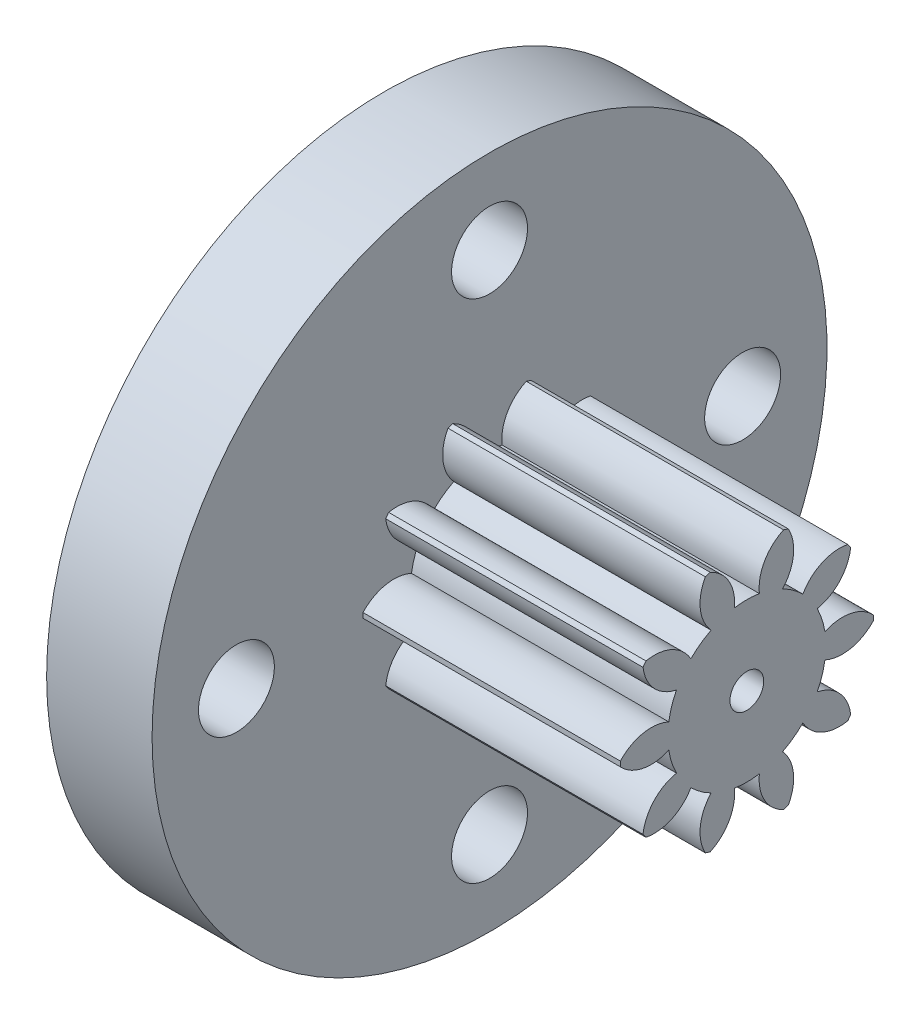
SolidWorks part; units mm, degrees
ref_plane "Plane1" through (0, 0, 0) normal (0, 0, 1) x (1, 0, 0)
ref_plane "Plane2" through (0, 0, 0) normal (0, 1, 0) x (1, 0, 0)
ref_plane "Plane3" through (0, 0, 0) normal (1, 0, 0) x (0, 0, -1)
sketch "HoldingSke" plane through (0, 0, 0) normal (0, 1, 0) x (1, 0, 0)
  line L0 (0, 0) -> (1.9696, -0.3473)
  line L1 (-15, 0) -> (100, 0) construction
  line L2 (0, 0) -> (-2.1039, 2.3779)
  line L3 (0, 0) -> (-11.863, 4.5341)
  line L4 (0, 0) -> (8.5048, 1.4996)
  line L5 (0, 0) -> (-46.8476, -17.4728)
  line L6 (0, 0) -> (-6.6317, -4.4744)
  line L7 (-2.1039, 2.3779) -> (8.6586, 51.2059)
  line L8 (-76.2, 54.61) -> (-76.1, 54.61)
  line L9 (-71.009, 38.7566) -> (-53.1078, 45.2721)
  line L10 (-76.2, 71.12) -> (104.1128, 71.12)
  line L11 (0, 0) -> (-8, 0)
  line L12 (-76.2, 101.6) -> (-76.181, 101.6)
  line L13 (24.9733, 27.94) -> (52.9518, 28.4284)
  line L14 (24.9733, 27.94) -> (24.9743, 27.94)
  line L15 (24.9733, 27.94) -> (100.4006, 29.5858)
  line L16 (-63.627, -0.5) -> (-12.827, -0.5)
  circle A0 centre (0, 0) radius 0.4
  circle A1 centre (0, 0) radius 1.874
  circle A2 centre (0, 0) radius 37.5
  circle A3 centre (0, 0) radius 0.4
  dimension "MHD" = 3.748
  dimension "Hub_dia" = 75
  dimension "Bore" = 0.8
  dimension "MBD" = 0.8
  dimension "Num_teeth" = 10
  dimension "Pitch" = 2
  dimension "Overall_len" = 50
  dimension "Show_teeth" = 10
  dimension "Thickness" = 8
  dimension "OAL" = 50.0001
  dimension "T_dim" = 0.1
  dimension "Ap" = 20
  dimension "H" = 19.05
  dimension "Pitch_radius" = 180.3128
  dimension "Width" = 8
  dimension "Backlash" = 0.019
  dimension "Addendum_fac" = 1
  dimension "Dedendum_fac" = 1.25
  dimension "Clearance_fac" = 0.25
  dimension "Dedendum_add" = 0.001
  dimension "Module" = 0.5
sketch "BasProSke" plane through (0, 0, 0) normal (0, 1, 0) x (1, 0, 0)
  line L0 (-10, 0) -> (60, 0) construction
  line L1 (0, 0) -> (0, 3)
  line L2 (0, 0) -> (8.6, 0)
  line L3 (8.6, 0) -> (8.6, 3)
  line L4 (8.6, 3) -> (0, 3)
  dimension "Thickness" = 8.6
  dimension "Diameter" = 6
revolve "Base-Revolve" add sketch "BasProSke" angle 360 about L0
sketch "TooCutSke" plane through (0, 0, 0) normal (1, 0, 0) x (0, 0, -1)
  line L1 (0, 0) -> (0, 107) construction
  line L2 (0, 0) -> (-0.4243, 2.4637) construction
  line L3 (0, 0) -> (-1.5292, 4.7063) construction
  line L4 (-0.4243, 2.4637) -> (-0.7646, 2.3532) construction
  arc A0 (0.2964, 1.8504) -> (-0.2964, 1.8504) centre (0, 0) ccw
  arc A1 (0.9059, 2.8866) -> (-0.9059, 2.8866) centre (0, 0) ccw
  circle A2 centre (0, 0) radius 2.5 construction
  circle A3 centre (0, 0) radius 2.3492 construction
  arc A4 (-0.2964, 1.8504) -> (-0.9059, 2.8866) centre (-1.2901, 1.9633) ccw
  arc A5 (0.9059, 2.8866) -> (0.2964, 1.8504) centre (1.2901, 1.9633) ccw
  dimension "Root_dia" = 3.748
  dimension "Overcut_dia" = 6.0508
  dimension "Pitch_dia" = 5
  dimension "Base_dia" = 4.6985
  dimension "Flank_rad" = 1
  dimension "Half_ang" = 18
  dimension "Half_CT" = 0.3578
extrude "ToothCut" cut sketch "TooCutSke" along normal through all
fillet "Breaks" [suppressed] radius 0.01
fillet "RootFillets" [suppressed] radius 0.126
pattern_circular "TeethCuts" count 10 over 360 about axis through (0, 0, 0) along (1, 0, 0) of "ToothCut", "RootFillets", "Breaks"
sketch "HubNeaOneSke" plane through (0, 0, 0) normal (-1, 0, 0) x (0, 0, 1)
  circle A0 centre (0, 0) radius 1.874
  dimension "Diameter" = 3.748
extrude "HubNearOne" [suppressed] add sketch "HubNeaOneSke" along normal blind 41.4001
sketch "HubNeaBotSke" plane through (0, 0, 0) normal (-1, 0, 0) x (0, 0, 1)
  circle A0 centre (0, 0) radius 1.874
  dimension "Diameter" = 3.748
extrude "HubNearBoth" [suppressed] add sketch "HubNeaBotSke" along normal blind 20.7
ref_plane "FarPln" through (8.6, 0, 0) normal (1, 0, 0) x (0, 0, -1)
sketch "HubFarSke" plane through (8.6, 0, 0) normal (1, 0, 0) x (0, 0, -1)
  circle A0 centre (0, 0) radius 1.874
  dimension "Diameter" = 3.748
extrude "HubFar" [suppressed] add sketch "HubFarSke" along normal blind 20.7
sketch "BorSke" plane through (0, 0, 0) normal (1, 0, 0) x (0, 0, -1)
  circle A0 centre (0, 0) radius 0.4
  dimension "Diameter" = 0.8
extrude "Bore" cut sketch "BorSke" along normal mid plane 100.0001
sketch "KeySke" plane through (0, 0, 0) normal (1, 0, 0) x (0, 0, -1)
  line L0 (-0.05, 0) -> (-0.05, 0.5)
  line L1 (-0.05, 0.5) -> (0.05, 0.5)
  line L2 (0.05, 0.5) -> (0.05, 0)
  line L3 (0, 0) -> (0, 34) construction
  line L4 (-0.05, 0) -> (0.05, 0)
  dimension "Offset" = 0.5
  dimension "Width" = 0.1
extrude "Keyway" [suppressed] cut sketch "KeySke" along normal mid plane 100.0001
pattern_circular "Keyway2" [suppressed] count 2 every 90 about axis through (-10, 0, 0) along (1, 0, 0)
sketch "Sketch1" plane through (0, 0, 0) normal (-1, 0, 0) x (0, 0, 1)
  circle A0 centre (0, 0) radius 8
  dimension "D1" = 16
extrude "Boss-Extrude1" add sketch "Sketch1" against normal blind 2.5
hole_wizard "M1.6 Clearance Hole1" positions "Sketch2" profile "Sketch3" hole size "M1.6" standard "ISO"
sketch "Sketch2" plane through (2.5, 0, 0) normal (1, 0, 0) x (0, 0, -1)
  line L0 (-15.5326, 0) -> (15.8639, 0) construction
  line L2 (0, 11.0318) -> (0, -13.9603) construction
  circle A0 centre (0, 0) radius 6 construction
  point P0 (0, 6)
  point P2 (6, 0)
  point P4 (0, -6)
  point P6 (-6, 0)
  dimension "D1" = 12
sketch "Sketch3" plane through (2.5, 6, 0) normal (0, 1, 0) x (0, 0, -1)
  line L0 (0, 0) -> (0, 4.7908)
  line L1 (0, 4.7908) -> (0.9, 4.25)
  line L2 (0.9, 4.25) -> (0.9, 0)
  line L5 (0.9, 0) -> (0, 0)
  line L10 (0, 4.7908) -> (-0.9, 4.25) construction
  line L11 (0, -6.35) -> (0, 107.95) construction
  dimension "Hole Dia." = 1.8
  dimension "Hole Depth" = 4.25
  dimension "Drill Angle" = 118
equation "' \"Module@HoldingSke\" = 6.35"
equation "' \"Num_teeth@HoldingSke\" = 12"
equation "' \"Ap@HoldingSke\" =  20"
equation "' \"Ap@HoldingSke\" = 20"
equation "' \"Width@HoldingSke\" = 0.5 * 25.4"
equation "' \"Hub_dia@HoldingSke\"= 1 * 25.4"
equation "' \"Hub_dia@HoldingSke\" = 1 * 25.4"
equation "' \"Overall_len@HoldingSke\" = 1.0 * 25.4"
equation "' \"Bore@HoldingSke\" = 0.75 * 25.4"
equation "' \"T_dim@HoldingSke\" = 0.1 * 25.4"
equation "' \"Width@KeySke\" = 0.25 * 25.4"
equation "' \"Show_teeth@HoldingSke\" = 13"
equation "' \"Backlash@HoldingSke\" = 0.009 * 25.4"
equation "' \"Addendum_fac@HoldingSke\" = 1.0"
equation "' \"Dedendum_fac@HoldingSke\" = 1.25"
equation "' \"Dedendum_add@HoldingSke\" = 0.00005 * 25.4"
equation "' \"Clearance_fac@HoldingSke\" = 0.25"
equation "\"Pitch@HoldingSke\" = 1 / \"Module@HoldingSke\""
equation "\"Overcut_dia@TooCutSke\" = (\"Num_teeth@HoldingSke\" + 2 * \"Addendum_fac@HoldingSke\") / \"Pitch@HoldingSke\" + 0.002 * 25.4"
equation "\"Pitch_dia@TooCutSke\" = \"Num_teeth@HoldingSke\" / \"Pitch@HoldingSke\""
equation "\"Base_dia@TooCutSke\" = \"Num_teeth@HoldingSke\" / \"Pitch@HoldingSke\" * cos((\"Ap@HoldingSke\"  * 3.14159265 / 180))"
equation "\"Root_dia@TooCutSke\" = (\"Num_teeth@HoldingSke\" + 2) / \"Pitch@HoldingSke\" - 2 * (\"Addendum_fac@HoldingSke\" + \"Dedendum_fac@HoldingSke\") / \"Pitch@HoldingSke\" - \"Dedendum_add@HoldingSke\" * 2"
equation "\"Half_ang@TooCutSke\" = 180 / \"Num_teeth@HoldingSke\""
equation "\"Half_CT@TooCutSke\" = \"Num_teeth@HoldingSke\" / \"Pitch@HoldingSke\" * sin((3.14159265 / 2 / \"Num_teeth@HoldingSke\")) / 2 - 7 * \"Backlash@HoldingSke\" / 4"
equation "\"Flank_rad@TooCutSke\" = \"Num_teeth@HoldingSke\" / \"Pitch@HoldingSke\" / 5"
equation "\"Radius@RootFillets\" = \"Clearance_fac@HoldingSke\" / \"Pitch@HoldingSke\" + \"Dedendum_add@HoldingSke\""
equation "\"Break_rad@Breaks\" = 0.02 / \"Pitch@HoldingSke\""
equation "\"Thickness@HoldingSke\" = \"Width@HoldingSke\""
equation "\"OAL@HoldingSke\" = \"Thickness@HoldingSke\""
equation "\"MHD@HoldingSke\" = (\"Num_teeth@HoldingSke\" + 2) / \"Pitch@HoldingSke\" - 2 * (\"Addendum_fac@HoldingSke\" + \"Dedendum_fac@HoldingSke\")  / \"Pitch@HoldingSke\" - \"Dedendum_add@HoldingSke\" * 2"
equation "\"MBD@HoldingSke\" = (\"Num_teeth@HoldingSke\" + 2) / \"Pitch@HoldingSke\" - 2 * (\"Addendum_fac@HoldingSke\" + \"Dedendum_fac@HoldingSke\")  / \"Pitch@HoldingSke\" - \"Dedendum_add@HoldingSke\" * 2 - 0.002 * 25.4"
equation "\"MHD@HoldingSke\" = ((sgn( \"MHD@HoldingSke\" - \"Hub_dia@HoldingSke\" )-1)*( \"MHD@HoldingSke\" - \"Hub_dia@HoldingSke\" ))/-2+ \"Hub_dia@HoldingSke\""
equation "\"MBD@HoldingSke\" = ((sgn( \"MBD@HoldingSke\" - \"Bore@HoldingSke\" )-1)*( \"MBD@HoldingSke\" - \"Bore@HoldingSke\" ))/-2+ \"Bore@HoldingSke\""
equation "\"OAL@HoldingSke\" = ((sgn( \"OAL@HoldingSke\" - \"Overall_len@HoldingSke\" )+1)*( \"OAL@HoldingSke\" - \"Overall_len@HoldingSke\" ))/2 + \"Overall_len@HoldingSke\" + 0.000002 * 25.4"
equation "\"Num_teeth@TeethCuts\" = int( \"Show_teeth@HoldingSke\" ) + 1"
equation "\"Num_teeth@TeethCuts\" = ((sgn( \"Num_teeth@TeethCuts\" - \"Num_teeth@HoldingSke\" )-1)*( \"Num_teeth@TeethCuts\" - \"Num_teeth@HoldingSke\" ))/-2+ \"Num_teeth@HoldingSke\""
equation "\"Num_teeth@TeethCuts\" = ((sgn( \"Num_teeth@TeethCuts\" - 2.0)+1)*( \"Num_teeth@TeethCuts\" - 2.0))/2 +2.0"
equation "\"Angle@TeethCuts\" = 360.0 / \"Num_teeth@HoldingSke\""
equation "\"Diameter@BasProSke\" = (\"Num_teeth@HoldingSke\" + 2 * \"Addendum_fac@HoldingSke\") / \"Pitch@HoldingSke\""
equation "\"Thickness@BasProSke\"=8.6"
equation "' \"Fillet_rad@BasProSke\" =  \"Thickness@HoldingSke\" * 0.05"
equation "' \"Fillet_rad@BasProSke\" = \"Thickness@HoldingSke\" * 0.05"
equation "\"MHD@HoldingSke\" = ((sgn( \"MHD@HoldingSke\" - \"Root_dia@TooCutSke\" )-1)*( \"MHD@HoldingSke\" - \"Root_dia@TooCutSke\" ))/-2+ \"Root_dia@TooCutSke\""
equation "\"Diameter@HubNeaOneSke\" = \"MHD@HoldingSke\""
equation "\"Length@HubNearOne\" = \"OAL@HoldingSke\" - \"Thickness@BasProSke\""
equation "\"Diameter@HubNeaBotSke\" = \"MHD@HoldingSke\""
equation "\"Length@HubNearBoth\" = ( \"OAL@HoldingSke\" - \"Thickness@BasProSke\" ) / 2.0"
equation "\"Thickness@FarPln\" = \"Thickness@BasProSke\""
equation "\"Diameter@HubFarSke\" = \"MHD@HoldingSke\""
equation "\"Length@HubFar\" = ( \"OAL@HoldingSke\" - \"Thickness@BasProSke\" ) / 2.0"
equation "\"Diameter@BorSke\" = \"MBD@HoldingSke\""
equation "\"D1@Bore\" = \"OAL@HoldingSke\" * 2.0"
equation "\"D1@Keyway\" = \"OAL@HoldingSke\" * 2.0"
equation "\"Offset@KeySke\" = \"T_dim@HoldingSke\" + \"MBD@HoldingSke\" / 2.0"
